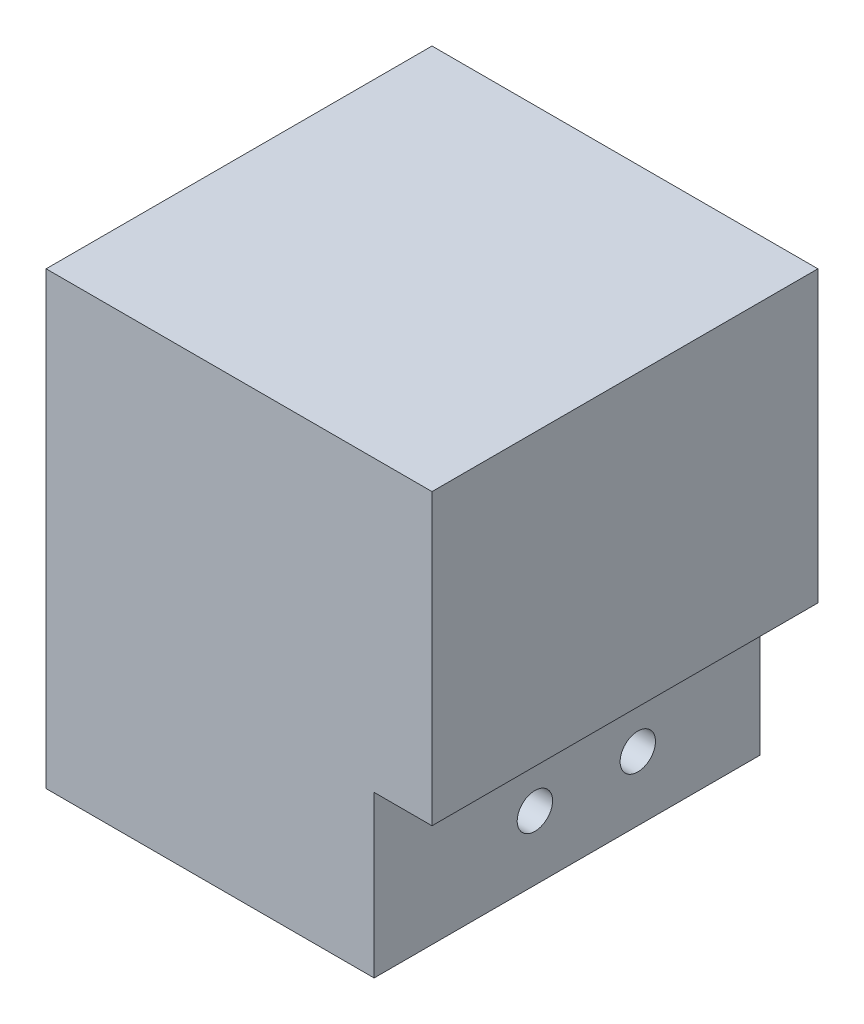
SolidWorks part; units mm, degrees
ref_plane "Front Plane" through (0, 0, 0) normal (0, 0, 1) x (1, 0, 0)
ref_plane "Top Plane" through (0, 0, 0) normal (0, 1, 0) x (1, 0, 0)
ref_plane "Right Plane" through (0, 0, 0) normal (1, 0, 0) x (0, 0, -1)
sketch "Sketch1" plane through (0, 0, 0) normal (0, 0, 1) x (1, 0, 0)
  line L1 (0, 0) -> (-60, 0)
  line L2 (0, 0) -> (0, 70)
  line L3 (0, 70) -> (-60, 70)
  line L4 (-60, 0) -> (-60, 70)
  dimension "D1" = 60
  dimension "D2" = 70
extrude "Boss-Extrude1" add sketch "Sketch1" along normal blind 60
sketch "Sketch2" plane through (0, 0, 0) normal (1, 0, 0) x (0, 0, -1)
  line L0 (-60, 0) -> (-60, 70) construction
  line L1 (-60, 25) -> (0, 25)
  line L2 (-60, 25) -> (-60, 0)
  line L3 (-60, 0) -> (0, 0)
  line L4 (0, 25) -> (0, 0)
  dimension "D1" = 25
extrude "Cut-Extrude1" cut sketch "Sketch2" against normal blind 9
hole_wizard "M5 Clearance Hole1" positions "3DSketch1" profile "Sketch11" hole size "M5" standard "ISO" end condition through all
sketch3d "3DSketch1"
  line L1 (-9, 25, 0) -> (-9, 25, 60) construction
  point P0 (-9, 10, 35)
  point P2 (-9, 10, 19)
  dimension "D1" = 25
  dimension "D2" = 16
  dimension "D3" = 15
  dimension "D4" = 15
sketch "Sketch11" plane through (-9, 10, 35) normal (0, 1, 0) x (0, 0, -1)
  line L0 (0, 0) -> (0, 51)
  line L1 (0, 51) -> (2.75, 51)
  line L2 (2.75, 51) -> (2.75, 0)
  line L5 (2.75, 0) -> (0, 0)
  line L11 (0, -6.35) -> (0, 107.95) construction
  dimension "Thru Hole Dia." = 5.5
  dimension "Thru Hole Depth" = 51
sketch "Sketch12" plane through (-60, 0, 0) normal (-1, 0, 0) x (0, 0, 1)
  circle A0 centre (19, 10) radius 6.75
  circle A1 centre (35, 10) radius 6.75
  dimension "D1" = 13.5
  dimension "D2" = 13.5
extrude "Cut-Extrude2" cut sketch "Sketch12" against normal blind 25
sketch "Sketch13" plane through (0, 70, 0) normal (0, 1, 0) x (1, 0, 0)
  line L0 (0, -60) -> (0, 0) construction
  line L1 (0, -60) -> (-60, -60) construction
  line L4 (-60, -15.0982) -> (-60, -60)
  line L5 (-60, -60) -> (-15.221, -60)
  line L6 (-60, -60) -> (-60, 0) construction
  arc A0 (-60, -15.0982) -> (-15.221, -60) centre (-70.3727, -70.2217) cw
  point P1 (-30.08, -31.2)
  point P10 (-15.221, -60)
  point P13 (-60, -15.0982)
  dimension "D1" = 30.08
  dimension "D2" = 44.9018
  dimension "D3" = 44.779
  dimension "D4" = 28.8
sketch "Sketch14" plane through (0, 0, 60) normal (0, 0, 1) x (1, 0, 0)
  line L0 (0, 25) -> (0, 70) construction
  line L1 (0, 70) -> (-60, 70) construction
  line L2 (-15.221, 70) -> (-15.22, 60.14)
  line L4 (-60, 70) -> (-60, 35.4467)
  line L5 (-15.221, 70) -> (-60, 70)
  line L6 (-60, 70) -> (-60, 0) construction
  arc A1 (-60, 35.4467) -> (-15.22, 60.14) centre (-145.7048, 243.8175) ccw
  point P0 (-15.22, 60.14)
  point P13 (-60, 35.4467)
  dimension "D1" = 15.22
  dimension "D2" = 9.86
  dimension "D7" = 34.5533
sketch "Sketch15" plane through (-60, 0, 0) normal (-1, 0, 0) x (0, 0, 1)
  line L0 (60, 70) -> (0, 70) construction
  line L1 (0, 70) -> (0, 0) construction
  line L2 (15.13, 32.01) -> (15.0982, 70)
  line L3 (15.0982, 70) -> (60, 70)
  line L5 (15.13, 32.01) -> (24.88, 31.8)
  line L6 (60, 70) -> (60, 35.4467)
  arc A0 (24.88, 31.8) -> (60, 35.4467) centre (14.3846, 303.8143) ccw
  point P0 (15.13, 32.01)
  point P1 (24.88, 31.8)
  dimension "D1" = 37.99
  dimension "D2" = 15.13
  dimension "D3" = 38.2
  dimension "D4" = 24.88
